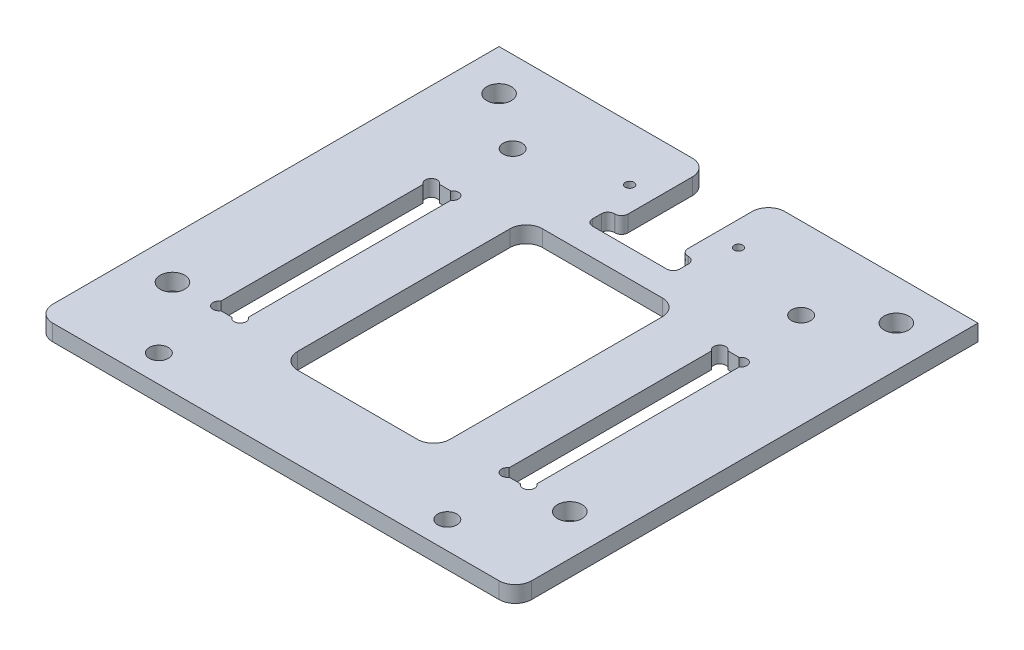
SolidWorks part; units mm, degrees
material "3.1325 (EN-AW 2017A)"
ref_plane "正面" through (0, 0, 0) normal (0, 0, 1) x (1, 0, 0)
ref_plane "平面" through (0, 0, 0) normal (0, 1, 0) x (1, 0, 0)
ref_plane "右側面" through (0, 0, 0) normal (1, 0, 0) x (0, 0, -1)
sketch "ｽｹｯﾁ1" plane through (0, 0, 0) normal (0, 1, 0) x (1, 0, 0)
  line L1 (-44, -42.5) -> (44, -42.5)
  line L2 (-44, -42.5) -> (-44, 42.5)
  line L3 (-44, 42.5) -> (44, 42.5)
  line L4 (44, -42.5) -> (44, 42.5)
  line L5 (-44, -42.5) -> (44, 42.5) construction
  line L6 (-44, 42.5) -> (44, -42.5) construction
  point P0 (0, 0)
  dimension "D1" = 85
  dimension "D2" = 88
extrude "ﾎﾞｽ - 押し出し1" add sketch "ｽｹｯﾁ1" along normal blind 3
sketch "ｽｹｯﾁ2" plane through (0, 3, 0) normal (0, 1, 0) x (1, 0, 0)
  line L0 (-23.95, -5) -> (23.95, -5) construction
  line L1 (-29.05, 15.1) -> (-23.95, 15.1)
  line L2 (-29.05, 15.1) -> (-29.05, -25.1)
  line L3 (-29.05, -25.1) -> (-23.95, -25.1)
  line L4 (-23.95, 15.1) -> (-23.95, -25.1)
  line L5 (23.95, 15.1) -> (29.05, 15.1)
  line L6 (23.95, 15.1) -> (23.95, -25.1)
  line L7 (23.95, -25.1) -> (29.05, -25.1)
  line L8 (29.05, 15.1) -> (29.05, -25.1)
  line L9 (-44, 42.5) -> (-44, -42.5) construction
  line L11 (44, -42.5) -> (44, 42.5) construction
  line L12 (44, 42.5) -> (-44, 42.5) construction
  line L14 (-26.5, 27.5) -> (-26.5, -37.5) construction
  line L15 (26.5, 27.5) -> (26.5, -37.5) construction
  line L16 (14, -27.5) -> (-14, -27.5)
  line L17 (14, -27.5) -> (14, 17.5)
  line L18 (14, 17.5) -> (-14, 17.5)
  line L19 (-14, -27.5) -> (-14, 17.5)
  line L20 (14, -27.5) -> (-14, 17.5) construction
  line L21 (14, 17.5) -> (-14, -27.5) construction
  circle A0 centre (-28.45, -24.5) radius 1.1
  circle A1 centre (-24.55, -24.5) radius 1.1
  circle A2 centre (-24.55, 14.5) radius 1.1
  circle A3 centre (-28.45, 14.5) radius 1.1
  circle A4 centre (28.45, 14.5) radius 1.1
  circle A5 centre (24.55, 14.5) radius 1.1
  circle A6 centre (24.55, -24.5) radius 1.1
  circle A7 centre (28.45, -24.5) radius 1.1
  circle A8 centre (-26.5, -37.5) radius 1.75
  circle A9 centre (26.5, -37.5) radius 1.75
  circle A10 centre (26.5, 27.5) radius 1.75
  circle A11 centre (-26.5, 27.5) radius 1.75
  circle A12 centre (-36.5, -25) radius 2.25
  circle A13 centre (36.5, -25) radius 2.25
  circle A14 centre (36.5, 35) radius 2.25
  circle A15 centre (-36.5, 35) radius 2.25
  point P33 (-26.5, -25.1)
  point P34 (26.5, -25.1)
  point P53 (0, -5)
  dimension "D11" = 32.5
  dimension "D12" = 2.2
  dimension "D13" = 3.5
  dimension "D16" = 60
  dimension "D17" = 0.6
  dimension "D18" = 0.6
  dimension "D6" = 0.6
  dimension "D19" = 0.6
  dimension "D20" = 0.6
  dimension "D21" = 0.6
  dimension "D22" = 7.5
  dimension "D23" = 4.5
  dimension "D27" = 7.5
  dimension "D28" = 7.5
  dimension "D29" = 7.5
  dimension "D31" = 28
  dimension "D2" = 40.2
  dimension "D3" = 5.1
  dimension "D4" = 5.1
  dimension "D5" = 40.2
  dimension "D7" = 0.6
  dimension "D30" = 26.5
  dimension "D32" = 45
  dimension "D14" = 32.5
  dimension "D15" = 5
  dimension "D8" = 2
  dimension "D9" = 2
  dimension "D10" = 2
  dimension "D25" = 2
  dimension "D26" = 2
extrude "ｶｯﾄ - 押し出し1" cut sketch "ｽｹｯﾁ2" against normal blind 3 contours A11 | A10 | A0 | A1 | L3 L4 L1 L2 | A3 | A2 | L8 L7 L6 L5 | A5 | A4 | A6 | A7 | A8 | A9 | A12 | A15 | A14 | A13 | L17 L16 L19 L18
sketch "ｽｹｯﾁ3" plane through (0, 3, 0) normal (0, 1, 0) x (1, 0, 0)
  line L0 (44, 42.5) -> (-44, 42.5) construction
  point P0 (-10, 32.5)
  point P1 (10, 32.5)
  point P4 (0, 42.5)
  point P5 (0, 0)
  point P7 (-52.2528, 41.9649)
  dimension "D1" = 20
  dimension "D2" = 10
  dimension "D3" = 10
hole_wizard "M2x0.4 ねじ穴1" positions "ｽｹｯﾁ3" profile "ｽｹｯﾁ4" tap size "M2x0.4" standard "JIS"
sketch "ｽｹｯﾁ4" plane through (-10, 3, -32.5) normal (1, 0, 0) x (0, 0, 1)
  line L0 (0, 0) -> (0, 6.4807)
  line L1 (0, 6.4807) -> (0.8, 6)
  line L2 (0.8, 6) -> (0.8, 0)
  line L5 (0.8, 0) -> (0, 0)
  line L10 (0, 6.4807) -> (-0.8, 6) construction
  line L11 (0, -6.35) -> (0, 107.95) construction
  dimension "ねじ下穴ﾄﾞﾘﾙ直径" = 1.6
  dimension "ねじ下穴ﾄﾞﾘﾙの深さ" = 6
  dimension "ﾄﾞﾘﾙ角度" = 118
cosmetic thread "穴のねじ山1" parameters "D1"=4, "D2"=2
cosmetic thread "穴のねじ山2" parameters "D1"=4, "D2"=2
sketch "ｽｹｯﾁ5" plane through (0, 3, 0) normal (0, 1, 0) x (1, 0, 0)
  line L0 (44, 42.5) -> (-44, 42.5) construction
  line L1 (-5.5, 42.5) -> (5.5, 42.5)
  line L2 (-5.5, 42.5) -> (-5.5, 26.5)
  line L3 (-5.5, 22.5) -> (5.5, 22.5)
  line L4 (5.5, 42.5) -> (5.5, 26.5)
  line L5 (-5.5, 42.5) -> (5.5, 22.5) construction
  line L6 (-5.5, 22.5) -> (5.5, 42.5) construction
  line L7 (-5.5, 23.125) -> (-5.5, 22.5) construction
  line L8 (-8, 22.5) -> (8, 22.5)
  line L9 (-8, 22.5) -> (-8, 26.5)
  line L10 (-8, 26.5) -> (-5.5, 26.5)
  line L11 (8, 22.5) -> (8, 26.5)
  line L12 (-8, 22.5) -> (8, 26.5) construction
  line L13 (-8, 26.5) -> (8, 22.5) construction
  line L14 (-5.5, 26.5) -> (-5.5, 25.875) construction
  line L15 (-5.5, 25.875) -> (-5.5, 23.125) construction
  line L16 (5.5, 23.125) -> (5.5, 22.5)
  line L17 (5.5, 25.875) -> (5.5, 23.125) construction
  line L18 (5.5, 26.5) -> (5.5, 25.875) construction
  line L19 (5.5, 26.5) -> (8, 26.5)
  line L20 (3.3, 26.5) -> (5.5, 26.5) construction
  line L21 (-3.3, 26.5) -> (3.3, 26.5) construction
  line L22 (-5.5, 26.5) -> (-3.3, 26.5) construction
  point P4 (0, 32.5)
  point P8 (0, 42.5)
  point P9 (0, 42.5)
  point P13 (0, 24.5)
  point P14 (0, 22.5)
  point P15 (0, 22.5)
  dimension "D1" = 11
  dimension "D2" = 20
  dimension "D3" = 4
  dimension "D4" = 16
extrude "ｶｯﾄ - 押し出し2" cut sketch "ｽｹｯﾁ5" against normal through all contours L2 L10 L9 L8 L11 L19 L4 L1
fillet "ﾌｨﾚｯﾄ7" radius 3 8 edges at (-14, 1.5, 27.5) (14, 1.5, 27.5) (14, 1.5, -17.5) (-14, 1.5, -17.5) (-5.5, 1.5, -42.5) (5.5, 1.5, -42.5) (44, 1.5, 42.5) (-44, 1.5, 42.5)
fillet "ﾌｨﾚｯﾄ6" radius 1.2 6 edges at (5.5, 1.5, -26.5) (8, 1.5, -26.5) (8, 1.5, -22.5) (-8, 1.5, -22.5) (-8, 1.5, -26.5) (-5.5, 1.5, -26.5)
